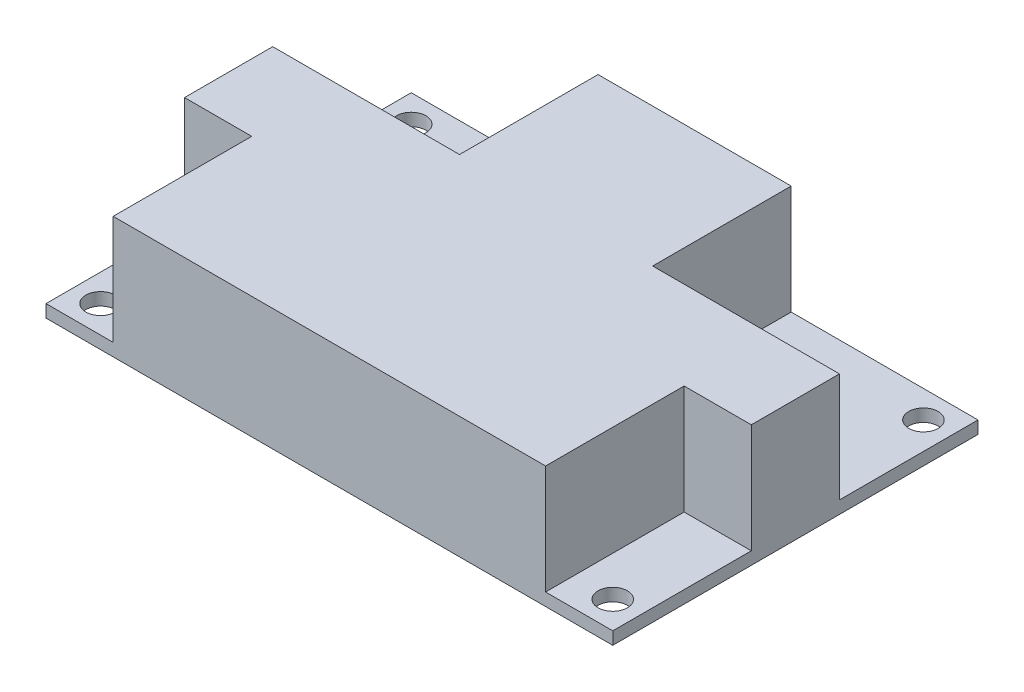
SolidWorks part; units mm, degrees
ref_plane "Plan de face" through (0, 0, 0) normal (0, 0, 1) x (1, 0, 0)
ref_plane "Plan de dessus" through (0, 0, 0) normal (0, 1, 0) x (1, 0, 0)
ref_plane "Plan de droite" through (0, 0, 0) normal (1, 0, 0) x (0, 0, -1)
sketch "Esquisse1" plane through (0, 0, 0) normal (0, 1, 0) x (1, 0, 0)
  line L0 (33.75, 43.5) -> (33.75, 0) construction
  line L1 (0, 0) -> (67.5, 0)
  line L2 (0, 0) -> (0, 43.5)
  line L3 (0, 43.5) -> (67.5, 43.5)
  line L4 (67.5, 0) -> (67.5, 43.5)
  line L5 (0, 21.75) -> (67.5, 21.75) construction
  line L7 (64.25, 3.25) -> (3.25, 3.25) construction
  line L8 (64.25, 3.25) -> (64.25, 40.25) construction
  line L9 (64.25, 40.25) -> (3.25, 40.25) construction
  line L10 (3.25, 3.25) -> (3.25, 40.25) construction
  line L11 (33.75, 40.25) -> (33.75, 3.25) construction
  line L12 (64.25, 21.75) -> (3.25, 21.75) construction
  circle A0 centre (3.25, 40.25) radius 1.75
  circle A1 centre (64.25, 40.25) radius 1.75
  circle A2 centre (64.25, 3.25) radius 1.75
  circle A3 centre (3.25, 3.25) radius 1.75
  point P9 (33.75, 21.75)
  dimension "D5" = 3.5
  dimension "D6" = 3.5
  dimension "D7" = 3.5
  dimension "D8" = 3.5
  dimension "D1" = 43.5
  dimension "D2" = 67.5
  dimension "D3" = 37
  dimension "D4" = 61
extrude "Boss.-Extru.1" add sketch "Esquisse1" along normal blind 1.5
sketch "Esquisse3" plane through (0, 1.5, 0) normal (0, 1, 0) x (1, 0, 0)
  line L0 (33.75, 43.5) -> (33.75, 0) construction
  line L1 (67.5, 43.5) -> (0, 43.5) construction
  line L2 (0, 0) -> (67.5, 0) construction
  line L3 (45.25, 43.5) -> (22.25, 43.5)
  line L4 (22.25, 43.5) -> (22.25, 27)
  line L5 (0, 27) -> (22.25, 27)
  line L6 (0, 43.5) -> (0, 0) construction
  line L7 (0, 27) -> (0, 16.5)
  line L8 (0, 16.5) -> (8, 16.5)
  line L9 (8, 16.5) -> (8, 0)
  line L10 (8, 0) -> (59.5, 0)
  line L11 (59.5, 16.5) -> (59.5, 0)
  line L12 (67.5, 16.5) -> (59.5, 16.5)
  line L13 (67.5, 27) -> (67.5, 16.5)
  line L14 (67.5, 27) -> (45.25, 27)
  line L15 (45.25, 43.5) -> (45.25, 27)
  point P14 (22.417, 26.7066)
  dimension "D1" = 23
  dimension "D2" = 16.5
  dimension "D3" = 16.5
  dimension "D4" = 8
extrude "Boss.-Extru.2" add sketch "Esquisse3" along normal blind 13
